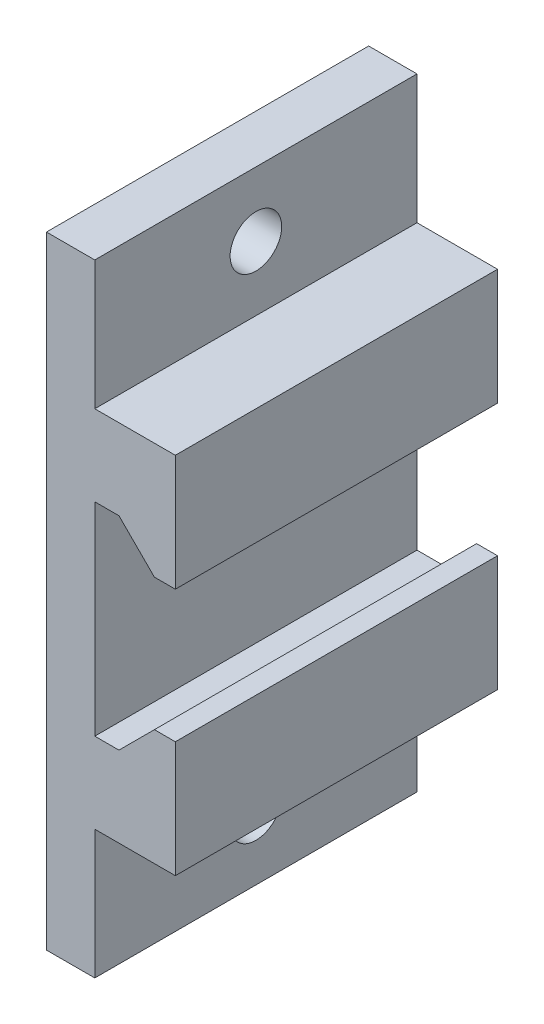
SolidWorks part; units mm, degrees
ref_plane "Front Plane" through (0, 0, 0) normal (0, 0, 1) x (1, 0, 0)
ref_plane "Top Plane" through (0, 0, 0) normal (0, 1, 0) x (1, 0, 0)
ref_plane "Right Plane" through (0, 0, 0) normal (1, 0, 0) x (0, 0, -1)
sketch "Sketch1" plane through (0, 0, 0) normal (0, 0, 1) x (1, 0, 0)
  line L0 (0, 19.3) -> (0, -19.3)
  line L1 (0, -19.3) -> (3, -19.3)
  line L2 (8, -11.3) -> (8, -4.1)
  line L3 (4.5, 6.3) -> (6.7, 4.1)
  line L4 (4.5, -6.3) -> (3, -6.3)
  line L5 (3, -6.3) -> (3, 6.3)
  line L6 (3, 6.3) -> (4.5, 6.3)
  line L7 (6.7, 4.1) -> (8, 4.1)
  line L8 (8, 4.1) -> (8, 11.3)
  line L9 (8, 11.3) -> (3, 11.3)
  line L10 (3, 11.3) -> (3, 19.3)
  line L11 (3, 19.3) -> (0, 19.3)
  line L12 (3, -19.3) -> (3, -11.3)
  line L13 (3, -11.3) -> (8, -11.3)
  line L15 (4.5, -6.3) -> (6.7, -4.1)
  line L16 (6.7, -4.1) -> (8, -4.1)
  point P14 (0, 0)
  point P15 (8.5935, -12.5)
  point P19 (0, 0)
  dimension "D1" = 3
  dimension "D2" = 1.5
  dimension "D3" = 45
  dimension "D4" = 8.2
  dimension "D5" = 5
  dimension "D6" = 1.3
  dimension "D7" = 5
  dimension "D8" = 8
  dimension "D9" = 38.6
extrude "Main" add sketch "Sketch1" along normal mid plane 20
sketch "Sketch2" plane through (3, 0, 0) normal (1, 0, 0) x (0, 0, -1)
  line L0 (-10, -19.3) -> (10, -19.3) construction
  line L1 (-10, 19.3) -> (10, 19.3) construction
  circle A0 centre (0, 15.3) radius 1.6
  circle A1 centre (0, -15.3) radius 1.6
  point P6 (0, 0)
  point P10 (0, 19.3)
  dimension "D1" = 3.2
  dimension "D2" = 4
  dimension "D3" = 4
extrude "Cut-Extrude1" cut sketch "Sketch2" against normal through all
